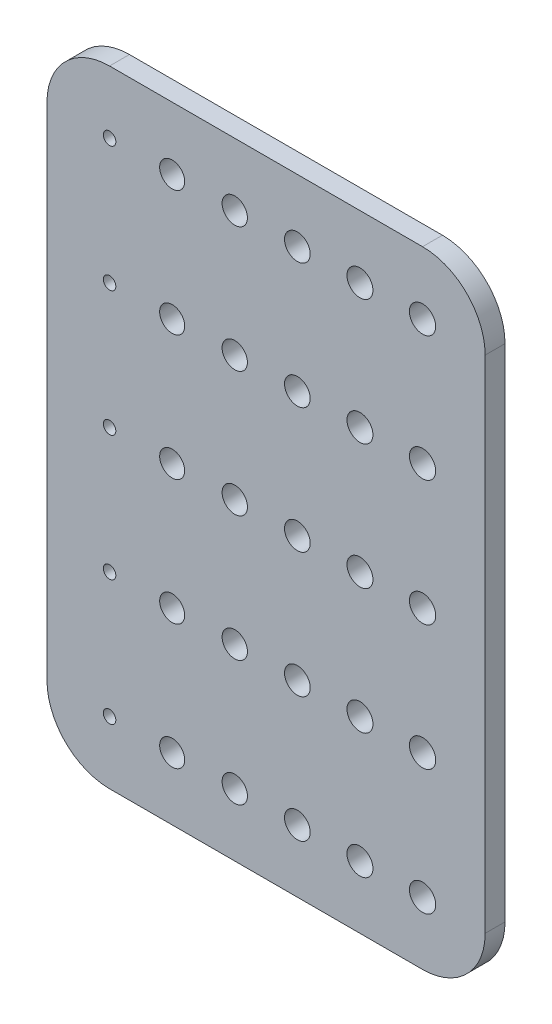
SolidWorks part; units mm, degrees
ref_plane "Front Plane" through (0, 0, 0) normal (0, 0, 1) x (1, 0, 0)
ref_plane "Top Plane" through (0, 0, 0) normal (0, 1, 0) x (1, 0, 0)
ref_plane "Right Plane" through (0, 0, 0) normal (1, 0, 0) x (0, 0, -1)
sketch "Sketch1" plane through (0, 0, 0) normal (0, 0, 1) x (1, 0, 0)
  line L0 (0, 0) -> (40, 0) construction
  line L2 (-20, 10) -> (50, 10)
  line L3 (-20, 10) -> (-20, -10)
  line L4 (-20, -10) -> (50, -10)
  line L5 (50, 10) -> (50, -10)
  circle A0 centre (0, 0) radius 2
  circle A1 centre (10, 0) radius 2.025
  circle A3 centre (20, 0) radius 2.05
  circle A4 centre (40, 0) radius 2.1
  circle A5 centre (30, 0) radius 2.075
  circle A6 centre (-10, 0) radius 1
  dimension "D1" = 4
  dimension "D2" = 4.05
  dimension "D3" = 10
  dimension "D4" = 4.1
  dimension "D5" = 4.15
  dimension "D6" = 4.2
  dimension "D7" = 2
  dimension "D8" = 10
  dimension "D9" = 10
  dimension "D10" = 10
  dimension "D11" = 10
  dimension "D12" = 10
  dimension "D13" = 10
  dimension "D14" = 10
  dimension "D15" = 10
extrude "Boss-Extrude1" add sketch "Sketch1" along normal blind 3.175
pattern_linear "LPattern1" count 5 spacing 20 along (0, -1, 0) of "Boss-Extrude1"
fillet "Fillet1" radius 10 4 edges at (50, 10, 1.5875) (-20, 10, 1.5875) (50, -90, 1.5875) (-20, -90, 1.5875)
